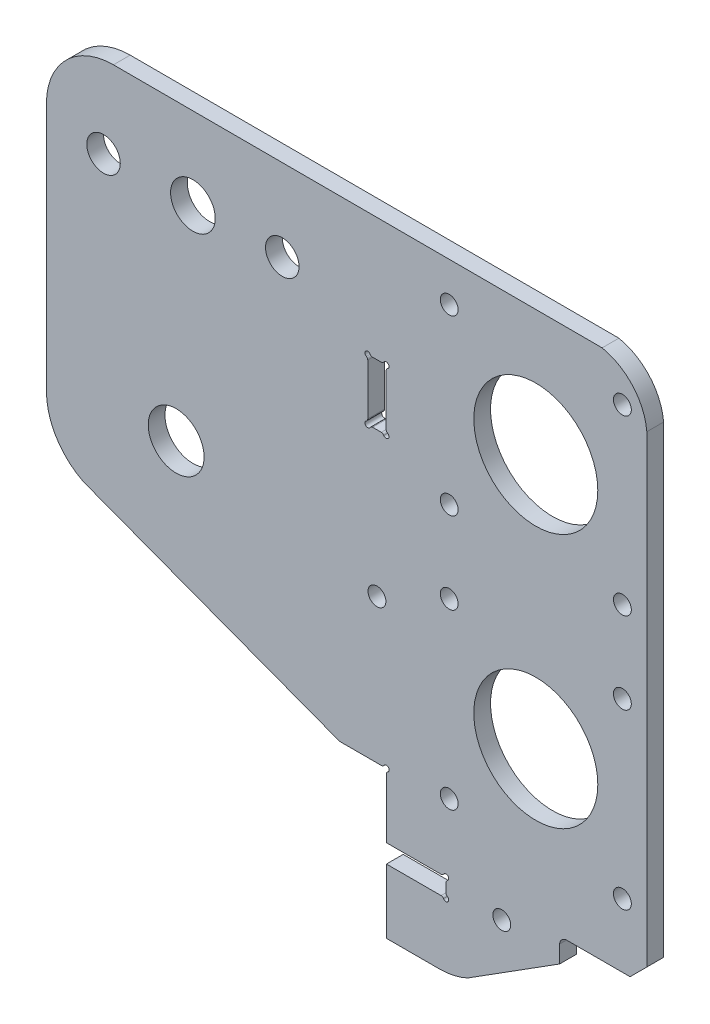
SolidWorks part; units mm, degrees
ref_plane "Front Plane" through (0, 0, 0) normal (0, 0, 1) x (1, 0, 0)
ref_plane "Top Plane" through (0, 0, 0) normal (0, 1, 0) x (1, 0, 0)
ref_plane "Right Plane" through (0, 0, 0) normal (1, 0, 0) x (0, 0, -1)
sketch "Sketch2" plane through (0, 0, 0) normal (0, 0, 1) x (1, 0, 0)
  line L0 (614.4351, 461.2252) -> (623.9033, 461.2247)
  line L1 (614.4351, 461.2252) -> (623.9033, 461.2247)
  line L2 (614.4378, 472.7498) -> (614.4351, 461.2252)
  line L3 (614.4378, 472.7498) -> (614.4351, 461.2252)
  line L4 (628.9814, 462.3521) -> (645.4378, 472.7494)
  line L5 (628.9814, 462.3521) -> (645.4378, 472.7494)
  line L6 (645.4378, 472.7494) -> (645.4378, 475.8423)
  line L7 (645.4378, 472.7494) -> (645.4378, 475.8423)
  line L8 (624.2199, 472.7497) -> (614.4378, 472.7498)
  line L9 (624.2199, 472.7497) -> (614.4378, 472.7498)
  line L10 (614.4379, 486.7091) -> (614.4379, 476.0497)
  line L11 (614.4379, 486.7091) -> (614.4379, 476.0497)
  line L12 (614.4379, 476.0497) -> (624.2207, 476.0496)
  line L13 (614.4379, 476.0497) -> (624.2207, 476.0496)
  line L14 (625.0865, 475.1834) -> (625.0862, 473.6155)
  line L15 (625.0865, 475.1834) -> (625.0862, 473.6155)
  line L16 (661.0539, 563.0849) -> (661.0532, 480.0849)
  line L17 (661.0539, 563.0849) -> (661.0532, 480.0849)
  line L18 (658.0532, 477.0849) -> (651.0532, 477.085)
  line L19 (658.0532, 477.0849) -> (651.0532, 477.085)
  line L20 (661.0532, 480.0849) -> (658.0532, 477.0849)
  line L21 (661.0532, 480.0849) -> (658.0532, 477.0849)
  line L22 (611.0937, 549.2245) -> (611.0937, 540.0914)
  line L25 (614.3934, 549.2248) -> (614.3934, 540.0911)
  line L27 (613.5274, 539.225) -> (611.9595, 539.225)
  line L31 (653.054, 572.085) -> (565.5686, 572.2252)
  line L32 (611.0808, 487.576) -> (613.5721, 487.5754)
  line L33 (606.0809, 487.576) -> (613.5721, 487.5754)
  line L34 (560.1702, 504.9001) -> (606.0809, 487.576)
  line L35 (560.1702, 504.9001) -> (606.0809, 487.576)
  line L38 (553.5685, 560.2254) -> (553.5682, 515.6176)
  line L41 (651.0532, 477.085) -> (646.6757, 477.085)
  line L51 (613.5274, 550.0908) -> (611.9595, 550.0908)
  arc A0 (623.9033, 461.2247) -> (628.9814, 462.3521) centre (623.9035, 473.2247) ccw
  arc A1 (623.9033, 461.2247) -> (628.9814, 462.3521) centre (623.9035, 473.2247) ccw
  arc A2 (624.6529, 472.4996) -> (625.3361, 473.1824) centre (625.086, 472.7495) ccw
  arc A3 (624.6529, 472.4996) -> (625.3361, 473.1824) centre (625.086, 472.7495) ccw
  arc A4 (624.6529, 472.4996) -> (624.2199, 472.7497) centre (624.2198, 472.2497) ccw
  arc A5 (624.6529, 472.4996) -> (624.2199, 472.7497) centre (624.2198, 472.2497) ccw
  circle A6 centre (635.0879, 474.3999) radius 1.6
  circle A7 centre (635.0879, 474.3999) radius 1.6
  arc A8 (624.2207, 476.0496) -> (624.6538, 476.2995) centre (624.2208, 476.5496) ccw
  arc A9 (624.2207, 476.0496) -> (624.6538, 476.2995) centre (624.2208, 476.5496) ccw
  arc A10 (625.3366, 475.6163) -> (624.6538, 476.2995) centre (625.0867, 476.0494) ccw
  arc A11 (625.3366, 475.6163) -> (624.6538, 476.2995) centre (625.0867, 476.0494) ccw
  arc A12 (625.3366, 475.6163) -> (625.0865, 475.1834) centre (625.5865, 475.1833) ccw
  arc A13 (625.3366, 475.6163) -> (625.0865, 475.1834) centre (625.5865, 475.1833) ccw
  arc A14 (625.0862, 473.6155) -> (625.3361, 473.1824) centre (625.5862, 473.6154) ccw
  arc A15 (625.0862, 473.6155) -> (625.3361, 473.1824) centre (625.5862, 473.6154) ccw
  circle A16 centre (656.6763, 488.4875) radius 1.6
  circle A17 centre (656.6763, 488.4875) radius 1.6
  circle A18 centre (625.6763, 488.4875) radius 1.6
  circle A19 centre (625.6763, 488.4875) radius 1.6
  arc A20 (646.6757, 477.085) -> (645.4378, 475.8423) centre (646.7832, 475.74) ccw
  arc A21 (646.6757, 477.085) -> (645.4378, 475.8423) centre (646.7832, 475.74) ccw
  arc A22 (661.0539, 563.0849) -> (653.054, 572.085) centre (651.0126, 562.2149) ccw
  circle A23 centre (625.6763, 534.0941) radius 1.6
  arc A24 (614.3934, 540.0911) -> (614.6434, 539.658) centre (614.8934, 540.0911) ccw
  circle A25 centre (625.6763, 534.0941) radius 1.6
  arc A26 (613.9604, 538.975) -> (614.6434, 539.658) centre (614.3934, 539.225) ccw
  circle A27 centre (641.1763, 549.5941) radius 11.1
  arc A28 (613.9604, 538.975) -> (613.5274, 539.225) centre (613.5274, 538.725) ccw
  arc A30 (611.9595, 539.225) -> (611.5264, 538.9751) centre (611.9594, 538.725) ccw
  circle A31 centre (641.1763, 549.5941) radius 11.1
  arc A32 (610.8436, 539.6583) -> (611.5264, 538.9751) centre (611.0935, 539.2252) ccw
  arc A34 (610.8436, 539.6583) -> (611.0937, 540.0914) centre (610.5937, 540.0914) ccw
  circle A35 centre (612.7431, 513.3999) radius 1.6
  circle A36 centre (612.7431, 513.3999) radius 1.6
  arc A37 (613.5721, 487.5754) -> (614.0052, 487.8253) centre (613.5722, 488.0754) ccw
  arc A38 (613.5721, 487.5754) -> (614.0052, 487.8253) centre (613.5722, 488.0754) ccw
  arc A39 (614.688, 487.1421) -> (614.0052, 487.8253) centre (614.4381, 487.5752) ccw
  arc A40 (614.688, 487.1421) -> (614.0052, 487.8253) centre (614.4381, 487.5752) ccw
  arc A41 (614.688, 487.1421) -> (614.4379, 486.7091) centre (614.9379, 486.709) ccw
  arc A42 (614.688, 487.1421) -> (614.4379, 486.7091) centre (614.9379, 486.709) ccw
  circle A43 centre (656.6763, 519.4875) radius 1.6
  circle A44 centre (656.6763, 519.4875) radius 1.6
  circle A45 centre (641.1763, 503.9875) radius 11.1
  circle A46 centre (641.1763, 503.9875) radius 11.1
  circle A47 centre (625.6763, 519.4875) radius 1.6
  circle A48 centre (625.6763, 519.4875) radius 1.6
  arc A49 (565.5686, 572.2252) -> (553.5685, 560.2254) centre (565.5685, 560.2252) ccw
  circle A50 centre (595.7931, 557.5299) radius 3
  arc A51 (553.5682, 515.6176) -> (560.1702, 504.9001) centre (565.5682, 515.6174) ccw
  circle A52 centre (656.6763, 534.0941) radius 1.6
  circle A53 centre (576.7931, 519.5299) radius 5
  circle A54 centre (579.7931, 557.5299) radius 4
  circle A55 centre (563.7931, 557.5299) radius 3
  arc A56 (610.8436, 549.6576) -> (611.0937, 549.2245) centre (610.5937, 549.2245) cw
  circle A57 centre (656.6763, 534.0941) radius 1.6
  arc A58 (610.8436, 549.6576) -> (611.5264, 550.3407) centre (611.0935, 550.0906) cw
  circle A59 centre (625.6763, 565.0941) radius 1.6
  arc A60 (611.9595, 550.0908) -> (611.5264, 550.3407) centre (611.9594, 550.5908) cw
  circle A61 centre (625.6763, 565.0941) radius 1.6
  arc A62 (613.9604, 550.3408) -> (613.5274, 550.0908) centre (613.5274, 550.5908) cw
  circle A63 centre (656.6763, 565.0941) radius 1.6
  arc A64 (613.9604, 550.3408) -> (614.6434, 549.6578) centre (614.3934, 550.0908) cw
  circle A65 centre (656.6763, 565.0941) radius 1.6
  arc A66 (614.3934, 549.2248) -> (614.6434, 549.6578) centre (614.8934, 549.2248) cw
  point P82 (0, 0)
  point P94 (0, 0)
  point P114 (0, 0)
  point P128 (0, 0)
  point P143 (613.5274, 550.0908)
  point P144 (0, 0)
  point P145 (0, 0)
  point P146 (0, 0)
  point P147 (0, 0)
  point P148 (0, 0)
  point P149 (614.3934, 549.2248)
  dimension "D3" = 22.2
extrude "Boss-Extrude1" add sketch "Sketch2" along normal blind 3
